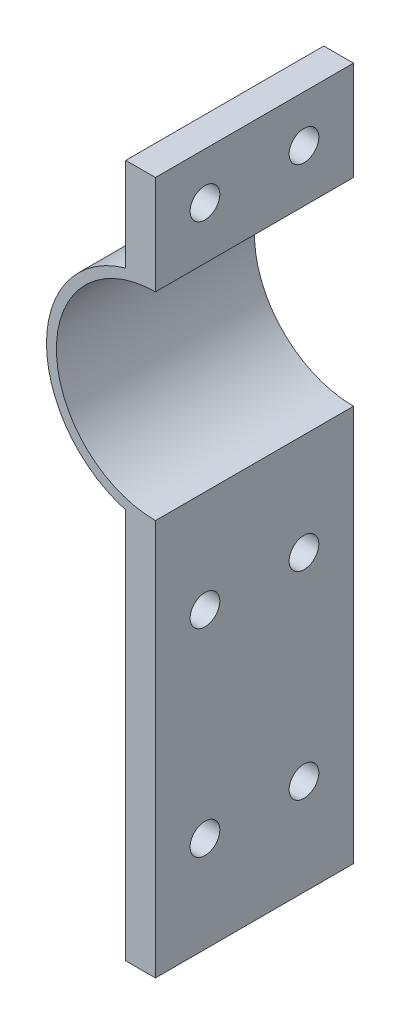
SolidWorks part; units mm, degrees
ref_plane "前视基准面" through (0, 0, 0) normal (0, 0, 1) x (1, 0, 0)
ref_plane "上视基准面" through (0, 0, 0) normal (0, 1, 0) x (1, 0, 0)
ref_plane "右视基准面" through (0, 0, 0) normal (1, 0, 0) x (0, 0, -1)
sketch "草图1" plane through (0, 0, 0) normal (0, 0, 1) x (1, 0, 0)
  line L0 (0, -50) -> (-3, -50)
  line L1 (0, 10) -> (0, 20)
  line L2 (0, -50) -> (0, -10)
  line L3 (-3, -50) -> (-3, -10.583)
  line L4 (0, 20) -> (-3, 20)
  line L5 (-3, 20) -> (-3, 10.583)
  arc A0 (0, 10) -> (0, -10) centre (0, 0) ccw
  arc A1 (-3, 10.583) -> (-3, -10.583) centre (0, 0) ccw
extrude "凸台-拉伸1" add sketch "草图1" along normal blind 20 contours L5 A1 L3 L0 L2 A0 L1 L4
ref_plane "基准面1" through (-3, 0, 0) normal (-1, 0, 0) x (0, 0, 1)
sketch "草图2" plane through (-3, 0, 0) normal (-1, 0, 0) x (0, 0, 1)
  circle A0 centre (5, 15.2915) radius 1.5
  circle A1 centre (15, 15.2915) radius 1.5
  circle A2 centre (5, -20.2915) radius 1.5
  circle A3 centre (15, -20.2915) radius 1.5
  circle A8 centre (15, -40.2915) radius 1.5
  circle A9 centre (5, -40.2915) radius 1.5
extrude "切除-拉伸1" cut sketch "草图2" against normal blind 20
